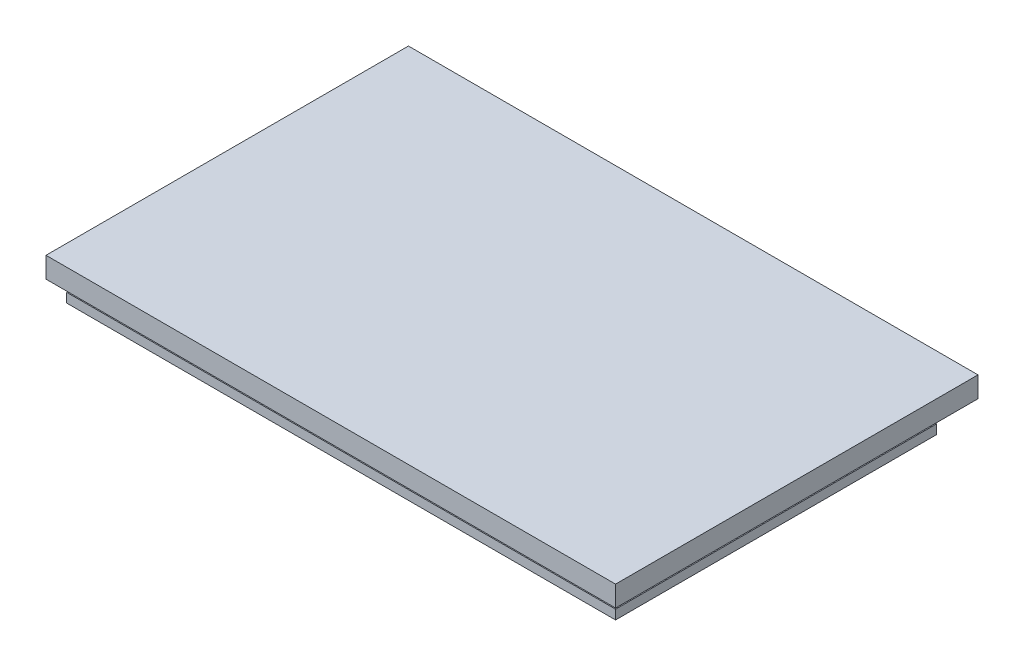
SolidWorks part; units mm, degrees
ref_plane "Front Plane" through (0, 0, 0) normal (0, 0, 1) x (1, 0, 0)
ref_plane "Top Plane" through (0, 0, 0) normal (0, 1, 0) x (1, 0, 0)
ref_plane "Right Plane" through (0, 0, 0) normal (1, 0, 0) x (0, 0, -1)
sketch "Sketch1" plane through (0, 0, 0) normal (0, 1, 0) x (1, 0, 0)
  line L1 (4.9268, 27.3028) -> (139.5468, 27.3028)
  line L2 (4.9268, 27.3028) -> (4.9268, -51.4372)
  line L3 (4.9268, -51.4372) -> (139.5468, -51.4372)
  line L4 (139.5468, 27.3028) -> (139.5468, -51.4372)
  dimension "D1" = 78.74
  dimension "D2" = 134.62
extrude "Boss-Extrude1" add sketch "Sketch1" along normal blind 2.286
sketch "Sketch2" plane through (0, 2.286, 0) normal (0, 1, 0) x (1, 0, 0)
  line L1 (4.9268, 22.2228) -> (134.4668, 22.2228)
  line L2 (4.9268, 22.2228) -> (4.9268, -46.3572)
  line L3 (4.9268, -46.3572) -> (134.4668, -46.3572)
  line L4 (134.4668, 22.2228) -> (134.4668, -46.3572)
  line L6 (4.9268, 27.3028) -> (4.9268, -51.4372) construction
  line L8 (139.5468, 27.3028) -> (4.9268, 27.3028) construction
  line L9 (4.9268, -51.4372) -> (139.5468, -51.4372) construction
  line L10 (139.5468, -51.4372) -> (139.5468, 27.3028) construction
  dimension "D1" = 5.08
  dimension "D2" = 5.08
  dimension "D3" = 5.08
extrude "Boss-Extrude2" add sketch "Sketch2" along normal blind 5.334
sketch "Sketch3" plane through (0, 7.62, 0) normal (0, 1, 0) x (1, 0, 0)
  line L0 (4.9268, 22.2228) -> (4.9268, -46.3572) construction
  line L1 (4.9268, 32.3828) -> (144.6268, 32.3828)
  line L2 (4.9268, 32.3828) -> (4.9268, -56.5172)
  line L3 (4.9268, -56.5172) -> (144.6268, -56.5172)
  line L4 (144.6268, 32.3828) -> (144.6268, -56.5172)
  line L6 (134.4668, 22.2228) -> (4.9268, 22.2228) construction
  line L7 (4.9268, -46.3572) -> (134.4668, -46.3572) construction
  line L8 (134.4668, -46.3572) -> (134.4668, 22.2228) construction
  point P8 (74.7768, -56.5172)
  dimension "D1" = 10.16
  dimension "D2" = 10.16
  dimension "D3" = 10.16
extrude "Boss-Extrude3" add sketch "Sketch3" along normal blind 5.08
